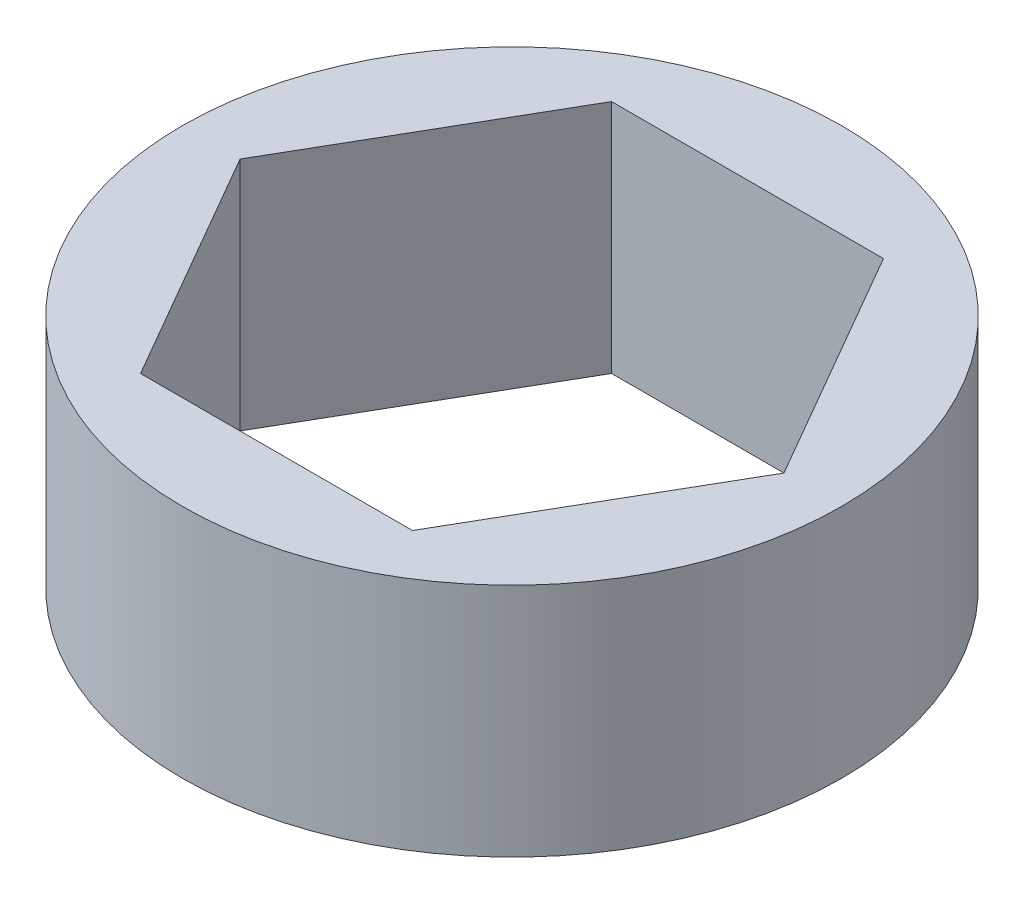
SolidWorks part; units mm, degrees
ref_plane "Front Plane" through (0, 0, 0) normal (0, 0, 1) x (1, 0, 0)
ref_plane "Top Plane" through (0, 0, 0) normal (0, 1, 0) x (1, 0, 0)
ref_plane "Right Plane" through (0, 0, 0) normal (1, 0, 0) x (0, 0, -1)
sketch "Sketch1" plane through (0, 0, 0) normal (0, 1, 0) x (1, 0, 0)
  line L1 (7.3323, 0) -> (3.6662, 6.35)
  line L2 (3.6662, 6.35) -> (-3.6662, 6.35)
  line L3 (-3.6662, 6.35) -> (-7.3323, 0)
  line L4 (-7.3323, 0) -> (-3.6662, -6.35)
  line L5 (-3.6662, -6.35) -> (3.6662, -6.35)
  line L6 (3.6662, -6.35) -> (7.3323, 0)
  circle A0 centre (0, 0) radius 6.35 construction
  circle A1 centre (0, 0) radius 8.89
  dimension "D1" = 12.7
  dimension "D3" = 17.78
  dimension "D2" = 6.35
extrude "Boss-Extrude1" add sketch "Sketch1" along normal blind 6.35
